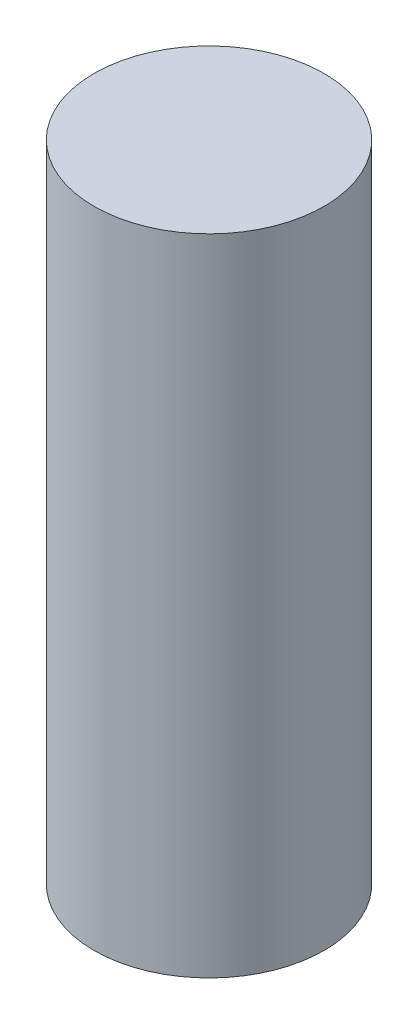
SolidWorks part; units mm, degrees
ref_plane "Plano frontal" through (0, 0, 0) normal (0, 0, 1) x (1, 0, 0)
ref_plane "Plano superior" through (0, 0, 0) normal (0, 1, 0) x (1, 0, 0)
ref_plane "Plano direito" through (0, 0, 0) normal (1, 0, 0) x (0, 0, -1)
sketch "Esboço1" plane through (0, 0, 0) normal (0, 1, 0) x (1, 0, 0)
  circle A0 centre (0, 0) radius 2
  dimension "D1" = 4
extrude "Ressalto-extrusão1" add sketch "Esboço1" along normal mid plane 11.2
